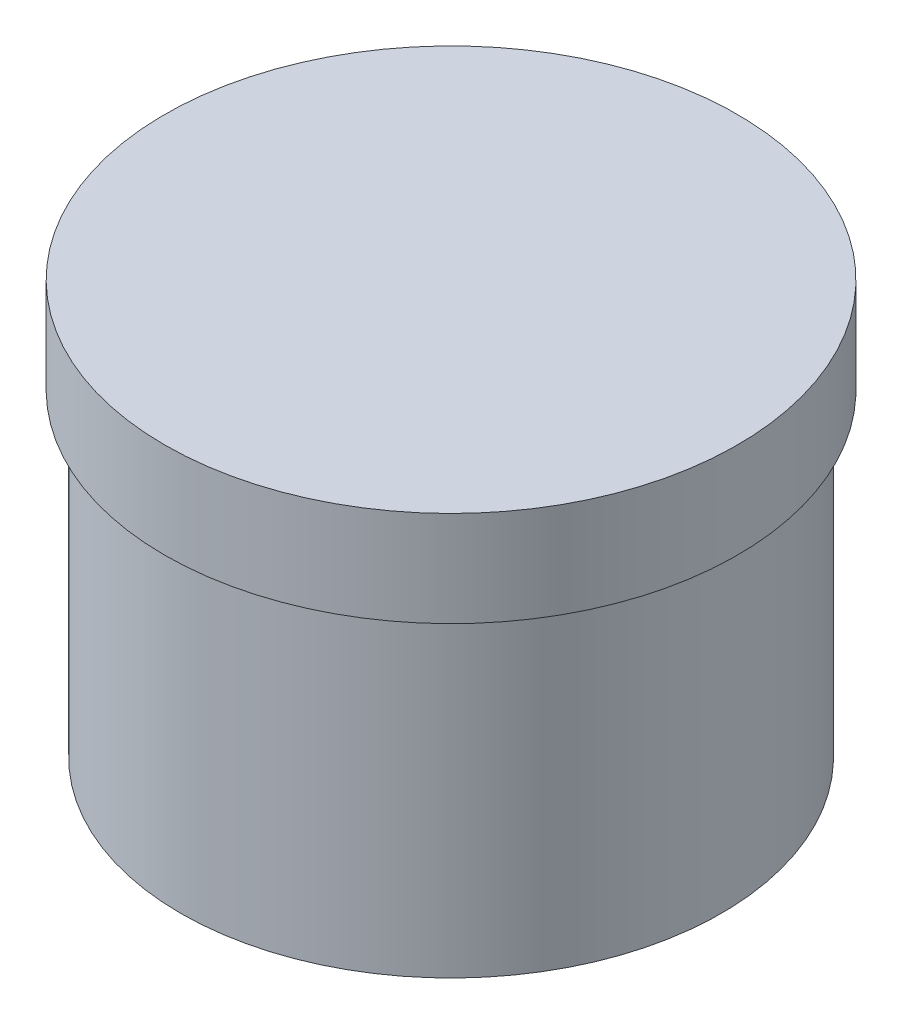
SolidWorks part; units mm, degrees
ref_plane "Front Plane" through (0, 0, 0) normal (0, 0, 1) x (1, 0, 0)
ref_plane "Top Plane" through (0, 0, 0) normal (0, 1, 0) x (1, 0, 0)
ref_plane "Right Plane" through (0, 0, 0) normal (1, 0, 0) x (0, 0, -1)
sketch "Sketch1" plane through (0, 0, 0) normal (0, 1, 0) x (1, 0, 0)
  circle A0 centre (0, 0) radius 42.5
  dimension "D1" = 85
extrude "Boss-Extrude1" add sketch "Sketch1" along normal blind 50
sketch "Sketch2" plane through (0, 50, 0) normal (0, 1, 0) x (1, 0, 0)
  circle A0 centre (0, 0) radius 45
  dimension "D1" = 90
extrude "Boss-Extrude2" add sketch "Sketch2" along normal blind 15
